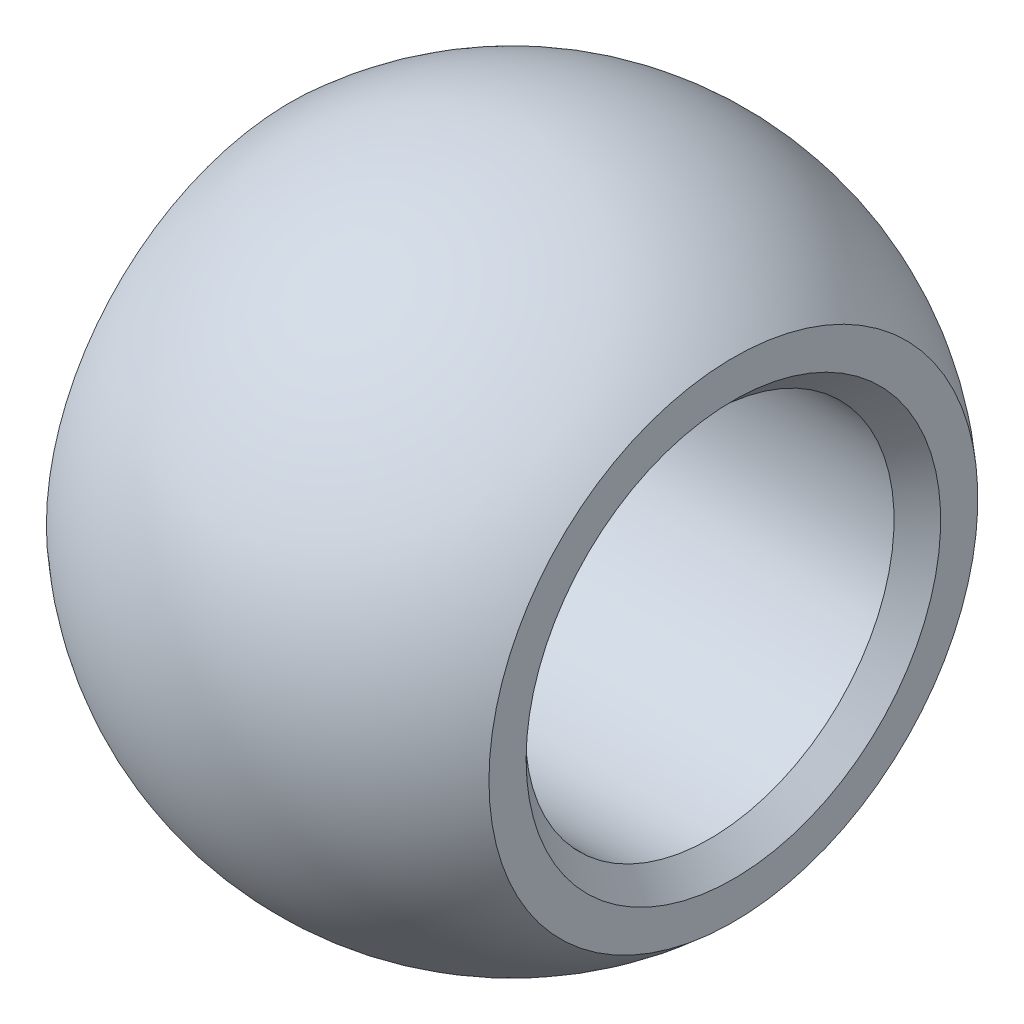
SolidWorks part; units mm, degrees
material "AISI 304"
ref_plane "Front Plane" through (0, 0, 0) normal (0, 0, 1) x (1, 0, 0)
ref_plane "Top Plane" through (0, 0, 0) normal (0, 1, 0) x (1, 0, 0)
ref_plane "Right Plane" through (0, 0, 0) normal (1, 0, 0) x (0, 0, -1)
sketch "Sketch1" plane through (0, 0, 0) normal (0, 0, 1) x (1, 0, 0)
  line L0 (-4.765, 0) -> (0, 0) construction
  line L1 (0, 0) -> (4.765, 0) construction
  line L2 (0, 0) -> (0, 3.97) construction
  line L3 (-4.255, 3.97) -> (4.255, 3.97)
  line L4 (4.765, 4.4635) -> (4.765, 5.2635)
  line L5 (-4.765, 4.4635) -> (-4.765, 5.2635)
  line L6 (-4.765, 4.4635) -> (-4.255, 3.97)
  line L7 (4.255, 3.97) -> (4.765, 4.4635)
  arc A0 (-4.765, 5.2635) -> (4.765, 5.2635) centre (0, 0) cw
  point P3 (-4.765, 3.97)
  point P6 (4.765, 3.97)
  point P7 (0, 0)
  point P10 (0, -0.1741)
  point P11 (0, 0)
  point P16 (0, 0)
  dimension "D1" = 7.1
  dimension "D2" = 7.94
  dimension "D3" = 9.53
  dimension "D4" = 0.8
revolve "Revolve1" add sketch "Sketch1" angle 360 about L0
